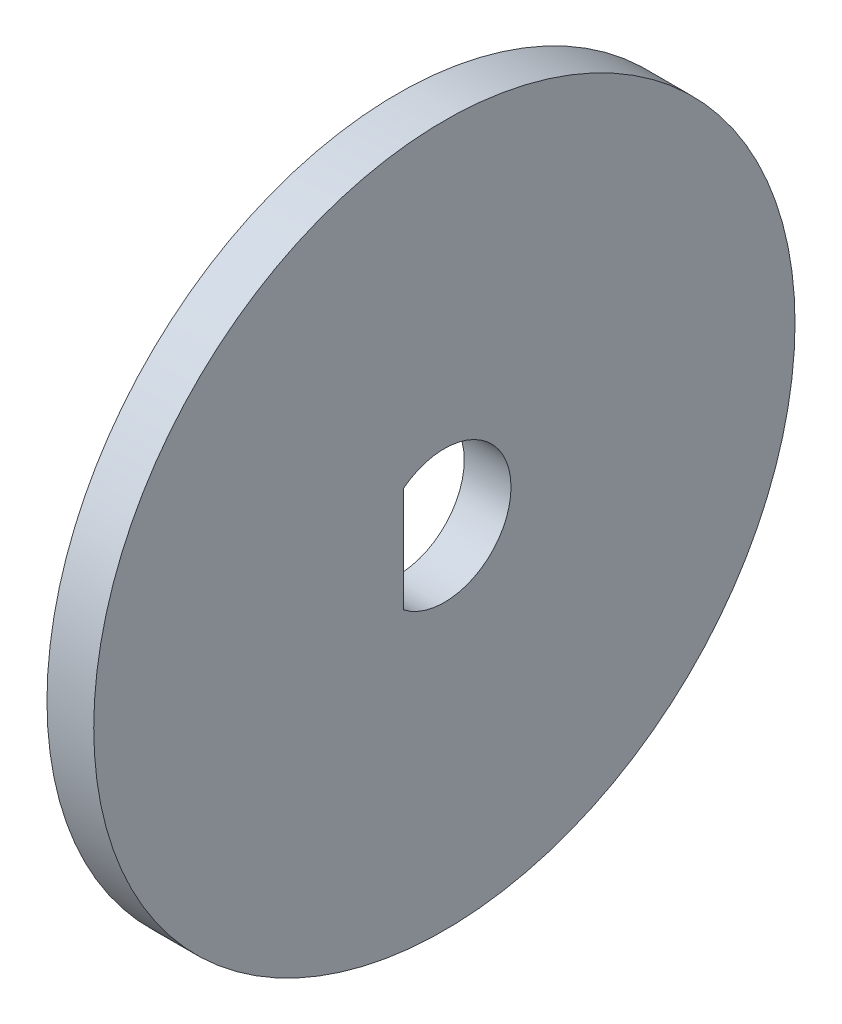
SolidWorks part; units mm, degrees
material "Pine"
ref_plane "Front Plane" through (0, 0, 0) normal (0, 0, 1) x (1, 0, 0)
ref_plane "Top Plane" through (0, 0, 0) normal (0, 1, 0) x (1, 0, 0)
ref_plane "Right Plane" through (0, 0, 0) normal (1, 0, 0) x (0, 0, -1)
sketch "Sketch1" plane through (0, 0, 0) normal (1, 0, 0) x (0, 0, -1)
  circle A0 centre (0, 0) radius 15
  dimension "D1" = 30
extrude "Boss-Extrude1" add sketch "Sketch1" along normal blind 2
sketch "Sketch2" plane through (2, 0, 0) normal (1, 0, 0) x (0, 0, -1)
  line L0 (-1.7493, 2.25) -> (-1.7493, -2.25)
  arc A0 (-1.7493, -2.25) -> (-1.7493, 2.25) centre (0, 0) ccw
  dimension "D1" = 5.7
  dimension "D2" = 4.5
extrude "Cut-Extrude1" cut sketch "Sketch2" against normal through all
